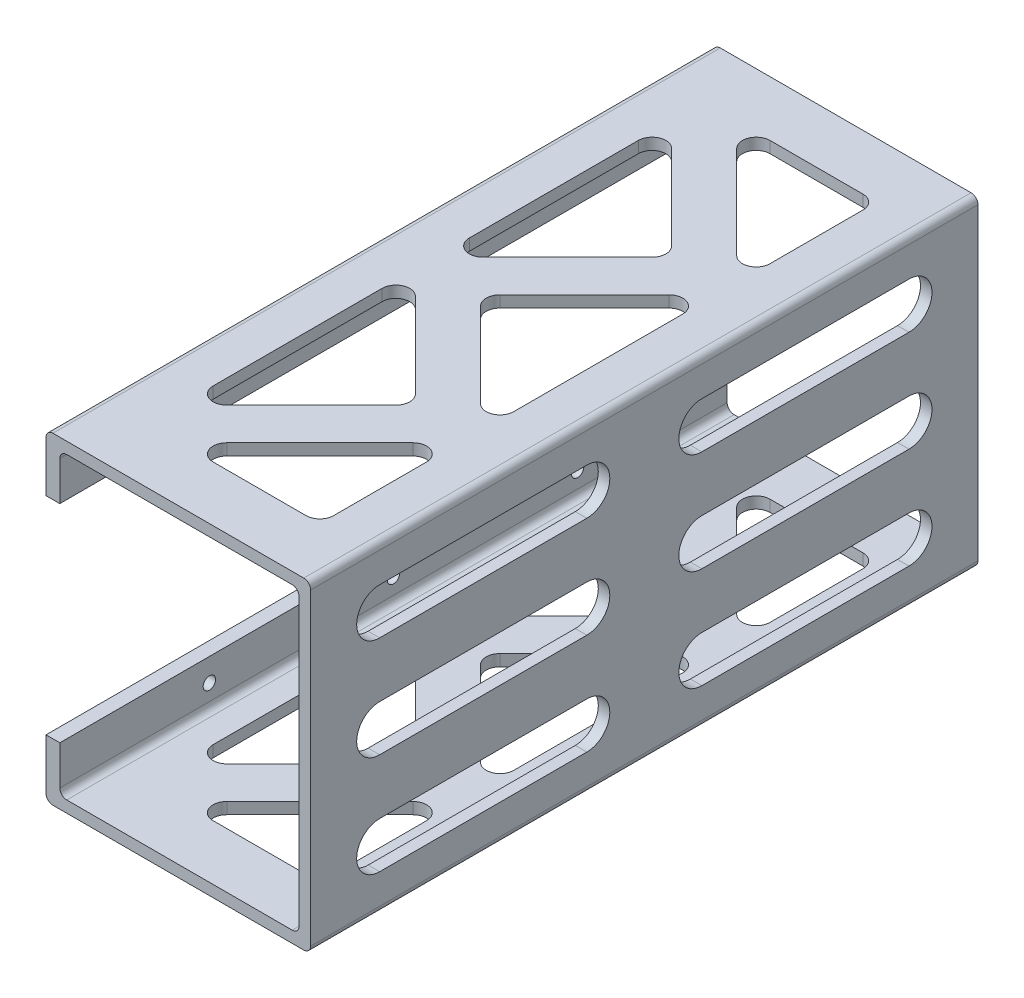
SolidWorks part; units mm, degrees
ref_plane "前视基准面" through (0, 0, 0) normal (0, 0, 1) x (1, 0, 0)
ref_plane "上视基准面" through (0, 0, 0) normal (0, 1, 0) x (1, 0, 0)
ref_plane "右视基准面" through (0, 0, 0) normal (1, 0, 0) x (0, 0, -1)
sketch "草图1" plane through (0, 0, 0) normal (0, 0, 1) x (1, 0, 0)
  line L0 (0, 57.5) -> (0, 70)
  line L2 (0, 70) -> (57.5, 70)
  line L3 (57.5, 70) -> (57.5, 0)
  line L4 (57.5, 0) -> (0, 0)
  line L5 (0, 0) -> (0, 12.5)
  line L6 (0, 12.5) -> (3, 12.5)
  line L7 (3, 12.5) -> (3, 2.5)
  line L8 (3, 2.5) -> (55, 2.5)
  line L9 (55, 2.5) -> (55, 67.5)
  line L10 (55, 67.5) -> (3, 67.5)
  line L11 (3, 67.5) -> (3, 57.5)
  line L12 (3, 57.5) -> (0, 57.5)
  point P2 (0, 0)
  dimension "D1" = 2.5
  dimension "D2" = 2.5
  dimension "D3" = 2.5
  dimension "D4" = 3
  dimension "D5" = 3
  dimension "D6" = 10
  dimension "D7" = 65
  dimension "D8" = 52
extrude "凸台-拉伸1" add sketch "草图1" against normal blind 145
sketch "草图2" plane through (0, 0, 0) normal (-1, 0, 0) x (0, 0, 1)
  line L0 (0, 67.5) -> (0, 2.5) construction
  line L1 (-112.5, 62.5) -> (-32.5, 62.5) construction
  line L2 (-112.5, 62.5) -> (-112.5, 7.5) construction
  line L3 (-112.5, 7.5) -> (-32.5, 7.5) construction
  line L4 (-32.5, 62.5) -> (-32.5, 7.5) construction
  line L5 (-112.5, 62.5) -> (-32.5, 7.5) construction
  line L6 (-112.5, 7.5) -> (-32.5, 62.5) construction
  line L9 (-145, 0) -> (0, 0) construction
  circle A2 centre (-112.5, 62.5) radius 1.35
  circle A3 centre (-72.5, 62.5) radius 1.35
  circle A4 centre (-32.5, 62.5) radius 1.35
  circle A5 centre (-32.5, 7.5) radius 1.35
  circle A6 centre (-72.5, 7.5) radius 1.35
  circle A7 centre (-112.5, 7.5) radius 1.35
  point P0 (-72.5, 35)
  dimension "D5" = 2.7
  dimension "D6" = 2.7
  dimension "D7" = 2.7
  dimension "D8" = 2.7
  dimension "D9" = 2.7
  dimension "D10" = 2.7
  dimension "D1" = 80
  dimension "D2" = 55
  dimension "D3" = 72.5
  dimension "D4" = 35
extrude "切除-拉伸1" cut sketch "草图2" against normal blind 3
sketch "草图3" plane through (55, 0, 0) normal (-1, 0, 0) x (0, 0, 1)
  line L0 (-130, 57) -> (-85, 57) construction
  line L1 (-130, 62) -> (-85, 62)
  line L2 (-130, 52) -> (-85, 52)
  line L3 (-130, 35) -> (-85, 35) construction
  line L4 (-130, 40) -> (-85, 40)
  line L5 (-130, 30) -> (-85, 30)
  line L6 (-130, 13) -> (-85, 13) construction
  line L7 (-130, 18) -> (-85, 18)
  line L8 (-130, 8) -> (-85, 8)
  line L9 (-60, 57) -> (-15, 57) construction
  line L10 (-60, 62) -> (-15, 62)
  line L11 (-60, 52) -> (-15, 52)
  line L12 (0, 67.5) -> (0, 2.5) construction
  line L13 (-130, 57) -> (-15, 57) construction
  line L14 (-130, 57) -> (-130, 13) construction
  line L15 (-130, 13) -> (-15, 13) construction
  line L16 (-15, 57) -> (-15, 13) construction
  line L17 (-145, 67.5) -> (-145, 2.5) construction
  line L18 (-145, 0) -> (0, 0) construction
  line L19 (-145, 70) -> (0, 70) construction
  line L20 (-60, 35) -> (-15, 35) construction
  line L23 (-60, 40) -> (-15, 40)
  line L24 (-60, 30) -> (-15, 30)
  line L25 (-60, 13) -> (-15, 13) construction
  line L26 (-60, 18) -> (-15, 18)
  line L27 (-60, 8) -> (-15, 8)
  arc A0 (-130, 62) -> (-130, 52) centre (-130, 57) ccw
  arc A1 (-85, 52) -> (-85, 62) centre (-85, 57) ccw
  arc A2 (-130, 40) -> (-130, 30) centre (-130, 35) ccw
  arc A3 (-85, 30) -> (-85, 40) centre (-85, 35) ccw
  arc A4 (-130, 18) -> (-130, 8) centre (-130, 13) ccw
  arc A5 (-85, 8) -> (-85, 18) centre (-85, 13) ccw
  arc A8 (-60, 62) -> (-60, 52) centre (-60, 57) ccw
  arc A9 (-15, 52) -> (-15, 62) centre (-15, 57) ccw
  arc A10 (-60, 40) -> (-60, 30) centre (-60, 35) ccw
  arc A11 (-15, 30) -> (-15, 40) centre (-15, 35) ccw
  arc A12 (-60, 18) -> (-60, 8) centre (-60, 13) ccw
  arc A13 (-15, 8) -> (-15, 18) centre (-15, 13) ccw
  point P2 (-107.5, 57)
  point P7 (-107.5, 35)
  point P14 (-107.5, 13)
  point P45 (-37.5, 57)
  point P53 (-37.5, 35)
  point P60 (-37.5, 13)
  dimension "D8" = 5
  dimension "D9" = 5
  dimension "D10" = 5
  dimension "D2" = 5
  dimension "D3" = 5
  dimension "D11" = 5
  dimension "D1" = 45
  dimension "D4" = 15
  dimension "D5" = 15
  dimension "D6" = 13
  dimension "D7" = 13
extrude "切除-拉伸2" cut sketch "草图3" against normal blind 2.5
sketch "草图4" plane through (0, 70, 0) normal (0, 1, 0) x (1, 0, 0)
  line L0 (57.5, 145) -> (0, 145) construction
  line L1 (17.0711, 133) -> (47.5, 133) construction
  line L3 (17.0711, 12) -> (47.5, 12) construction
  line L4 (47.5, 133) -> (47.5, 12) construction
  line L5 (10, 125.9289) -> (17.0711, 133) construction
  line L7 (10, 74.7377) -> (17.0711, 67.6667) construction
  line L8 (47.5, 98.0956) -> (21.9044, 72.5)
  line L9 (21.9044, 72.5) -> (47.5, 46.9044)
  line L10 (17.0711, 133) -> (47.5, 102.5711)
  line L11 (47.5, 102.5711) -> (47.5, 133)
  line L12 (47.5, 133) -> (17.0711, 133)
  line L13 (10, 125.9289) -> (35.5956, 100.3333)
  line L14 (35.5956, 100.3333) -> (10, 74.7377)
  line L15 (10, 70.2623) -> (35.5956, 44.6667)
  line L16 (35.5956, 44.6667) -> (10, 19.0711)
  line L17 (17.0711, 12) -> (47.5, 42.4289)
  line L18 (47.5, 42.4289) -> (47.5, 12)
  line L19 (47.5, 12) -> (17.0711, 12)
  line L20 (10, 125.9289) -> (10, 74.7377)
  line L21 (47.5, 98.0956) -> (47.5, 46.9044)
  line L22 (10, 70.2623) -> (10, 19.0711)
  line L23 (10, 70.2623) -> (17.0711, 77.3333) construction
  line L24 (10, 19.0711) -> (17.0711, 12) construction
  line L25 (47.5, 133) -> (10, 133) construction
  line L26 (57.5, 0) -> (0, 0) construction
  line L28 (57.5, 145) -> (57.5, 0) construction
  line L29 (10, 133) -> (10, 12) construction
  line L30 (10, 12) -> (47.5, 12) construction
  line L32 (0, 145) -> (0, 0) construction
  point P6 (17.5124, 74.1549)
  point P7 (18.9276, 74.3351)
  point P27 (13.0861, 7.5844)
  point P28 (21.4812, 76.1433)
  point P29 (15, 11.5583)
  point P30 (16.4282, 10)
  point P31 (19.406, 10)
  point P32 (0, 0)
  point P33 (16.4921, 69.9341)
  point P34 (19.9556, 69.9299)
  point P35 (0, 0)
  point P37 (0, 0)
  point P38 (11.8299, 17.9983)
  point P39 (20.0553, 67.4693)
  point P40 (28.3757, 104.2449)
  point P41 (10, 72.5)
  point P42 (25.0301, 72.5)
  point P45 (18.2393, 72.5)
  point P46 (36.9487, 39.1573)
  point P47 (21.4483, 72.5)
  dimension "D1" = 12
  dimension "D2" = 45
  dimension "D3" = 12
  dimension "D4" = 10
  dimension "D5" = 10
  dimension "D6" = 10
extrude "切除-拉伸3" cut sketch "草图4" against normal blind 70
fillet "圆角1" radius 3 30 edges at (47.5, 1.25, -12) (47.5, 1.25, -42.4289) (17.0711, 1.25, -12) (35.5956, 1.25, -44.6667) (10, 1.25, -70.2623) (10, 1.25, -19.0711) (47.5, 1.25, -46.9044) (47.5, 1.25, -98.0956) (21.9044, 1.25, -72.5) (10, 1.25, -74.7377) (35.5956, 1.25, -100.3333) (10, 1.25, -125.9289) (47.5, 1.25, -102.5711) (47.5, 1.25, -133) (17.0711, 1.25, -133) (47.5, 68.75, -133) (47.5, 68.75, -102.5711) (17.0711, 68.75, -133) (35.5956, 68.75, -100.3333) (10, 68.75, -125.9289) (10, 68.75, -74.7377) (47.5, 68.75, -98.0956) (47.5, 68.75, -46.9044) (21.9044, 68.75, -72.5) (35.5956, 68.75, -44.6667) (10, 68.75, -70.2623) (10, 68.75, -19.0711) (47.5, 68.75, -42.4289) (17.0711, 68.75, -12) (47.5, 68.75, -12)
fillet "圆角2" radius 1.5 8 edges at (57.5, 0, -72.5) (57.5, 70, -72.5) (0, 70, -72.5) (0, 0, -72.5) (3, 2.5, -72.5) (55, 2.5, -72.5) (55, 67.5, -72.5) (3, 67.5, -72.5)
